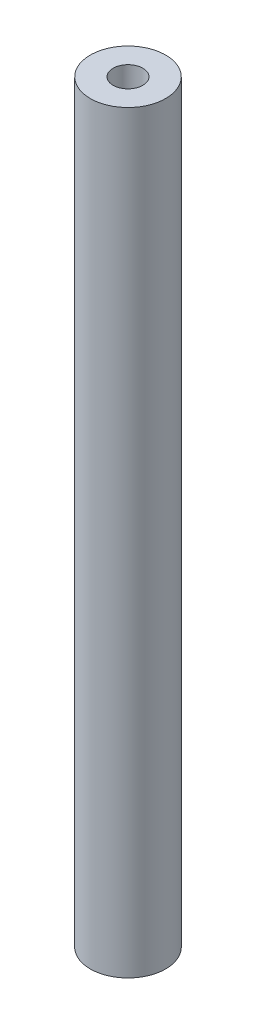
SolidWorks part; units mm, degrees
ref_plane "Front Plane" through (0, 0, 0) normal (0, 0, 1) x (1, 0, 0)
ref_plane "Top Plane" through (0, 0, 0) normal (0, 1, 0) x (1, 0, 0)
ref_plane "Right Plane" through (0, 0, 0) normal (1, 0, 0) x (0, 0, -1)
sketch "Sketch1" plane through (0, 0, 0) normal (0, 1, 0) x (1, 0, 0)
  circle A0 centre (0, 0) radius 3.175
  dimension "D1" = 6.35
extrude "Boss-Extrude1" add sketch "Sketch1" along normal blind 63.5
hole_wizard "M3x0.5 Tapped Hole1" positions "Sketch3" profile "Sketch2" tap size "M3x0.5" standard "ANSI Metric"
sketch "Sketch3" plane through (0, 63.5, 0) normal (0, 1, 0) x (1, 0, 0)
  point P0 (0, 0)
sketch "Sketch2" plane through (0, 63.5, 0) normal (1, 0, 0) x (0, 0, 1)
  line L0 (0, 0) -> (0, 13.4511)
  line L1 (0, 13.4511) -> (1.25, 12.7)
  line L2 (1.25, 12.7) -> (1.25, 0)
  line L5 (1.25, 0) -> (0, 0)
  line L10 (0, 13.4511) -> (-1.25, 12.7) construction
  line L11 (0, -6.35) -> (0, 107.95) construction
  dimension "Tap Drill Dia." = 2.5
  dimension "Tap Drill Depth" = 12.7
  dimension "Drill Angle" = 118
cosmetic thread "Hole Thread1"
hole_wizard "M3x0.5 Tapped Hole2" positions "Sketch5" profile "Sketch4" tap size "M3x0.5" standard "ANSI Metric"
sketch "Sketch5" plane through (0, 0, 0) normal (0, -1, 0) x (-1, 0, 0)
  point P0 (0, 0)
sketch "Sketch4" plane through (0, 0, 0) normal (1, 0, 0) x (0, 0, -1)
  line L0 (0, 0) -> (0, 13.4511)
  line L1 (0, 13.4511) -> (1.25, 12.7)
  line L2 (1.25, 12.7) -> (1.25, 0)
  line L5 (1.25, 0) -> (0, 0)
  line L10 (0, 13.4511) -> (-1.25, 12.7) construction
  line L11 (0, -6.35) -> (0, 107.95) construction
  dimension "Tap Drill Dia." = 2.5
  dimension "Tap Drill Depth" = 12.7
  dimension "Drill Angle" = 118
cosmetic thread "Hole Thread2" parameters "D1"=6.096, "D2"=3
